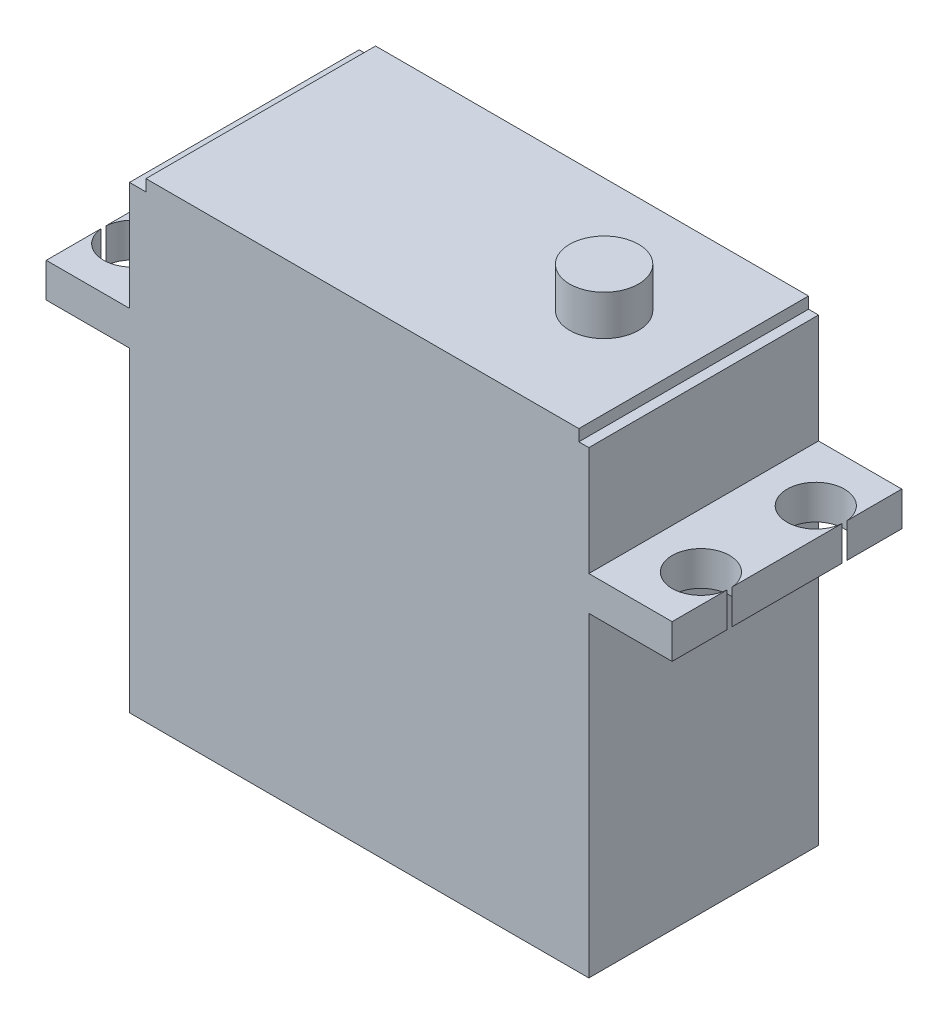
SolidWorks part; units mm, degrees
ref_plane "前视基准面" through (0, 0, 0) normal (0, 0, 1) x (1, 0, 0)
ref_plane "上视基准面" through (0, 0, 0) normal (0, 1, 0) x (1, 0, 0)
ref_plane "右视基准面" through (0, 0, 0) normal (1, 0, 0) x (0, 0, -1)
sketch "草图1" plane through (0, 0, 0) normal (0, 0, 1) x (1, 0, 0)
  line L0 (0, -22.5098) -> (0, 50.902) construction
  line L1 (20, 0) -> (-20, 0)
  line L2 (-20, 0) -> (-20, 27.5)
  line L3 (-20, 27.5) -> (-27.25, 27.5)
  line L4 (-27.25, 27.5) -> (-27.25, 30.5)
  line L5 (-27.25, 30.5) -> (-20, 30.5)
  line L6 (-20, 30.5) -> (-20, 40)
  line L7 (-20, 40) -> (20, 40)
  line L8 (20, 0) -> (20, 27.5)
  line L9 (20, 27.5) -> (27.25, 27.5)
  line L10 (27.25, 27.5) -> (27.25, 30.5)
  line L11 (27.25, 30.5) -> (20, 30.5)
  line L12 (20, 30.5) -> (20, 40)
  point P0 (0, 0)
  point P12 (0, 0)
  point P17 (0, 40)
  point P19 (0, 0)
  dimension "D1" = 40
  dimension "D2" = 7.25
  dimension "D3" = 7.25
  dimension "D4" = 27.5
  dimension "D5" = 40
  dimension "D6" = 3
extrude "凸台-拉伸1" add sketch "草图1" against normal blind 20
sketch "草图2" plane through (0, 30.5, 0) normal (0, 1, 0) x (1, 0, 0)
  line L0 (-27.25, 10) -> (27.25, 10) construction
  line L3 (-24.76, 22.1841) -> (-24.76, -1.904) construction
  line L4 (24.76, 22.1841) -> (24.76, -2.5762) construction
  line L5 (0, 24.0327) -> (0, -3.1364) construction
  line L6 (-27.25, 20) -> (-27.25, 0) construction
  line L7 (27.25, 20) -> (27.25, 0) construction
  circle A0 centre (-24.76, 15) radius 2.5
  circle A2 centre (-24.76, 5) radius 2.5
  circle A3 centre (24.76, 5) radius 2.5
  circle A4 centre (24.76, 15) radius 2.5
  dimension "D3" = 5
  dimension "D4" = 5
  dimension "D1" = 49.52
  dimension "D2" = 24.76
extrude "切除-拉伸4" cut sketch "草图2" against normal blind 20
sketch "草图3" plane through (0, 40, 0) normal (0, 1, 0) x (1, 0, 0)
  line L0 (-20, 10) -> (20, 10) construction
  line L1 (-20, 20) -> (-20, 0) construction
  line L2 (20, 20) -> (20, 0) construction
  line L4 (-18.5702, 20) -> (-18.5702, 0)
  line L5 (20, 20) -> (-20, 20) construction
  line L6 (20, 0) -> (-20, 0) construction
  line L7 (-18.5702, 0) -> (19.1304, 0)
  line L8 (19.1304, 0) -> (19.1304, 20)
  line L9 (19.1304, 20) -> (-18.5702, 20)
extrude "凸台-拉伸3" add sketch "草图3" along normal blind 1
sketch "草图4" plane through (0, 41, 0) normal (0, 1, 0) x (1, 0, 0)
  line L0 (-18.5702, 10) -> (19.1304, 10) construction
  line L1 (-18.5702, 20) -> (-18.5702, 0) construction
  line L2 (19.1304, 0) -> (19.1304, 20) construction
  line L3 (-18.5702, 20) -> (-18.5702, 0) construction
  circle A0 centre (11.3298, 10) radius 3
  dimension "D1" = 6
  dimension "D2" = 29.9
extrude "凸台-拉伸4" add sketch "草图4" along normal blind 3.5
